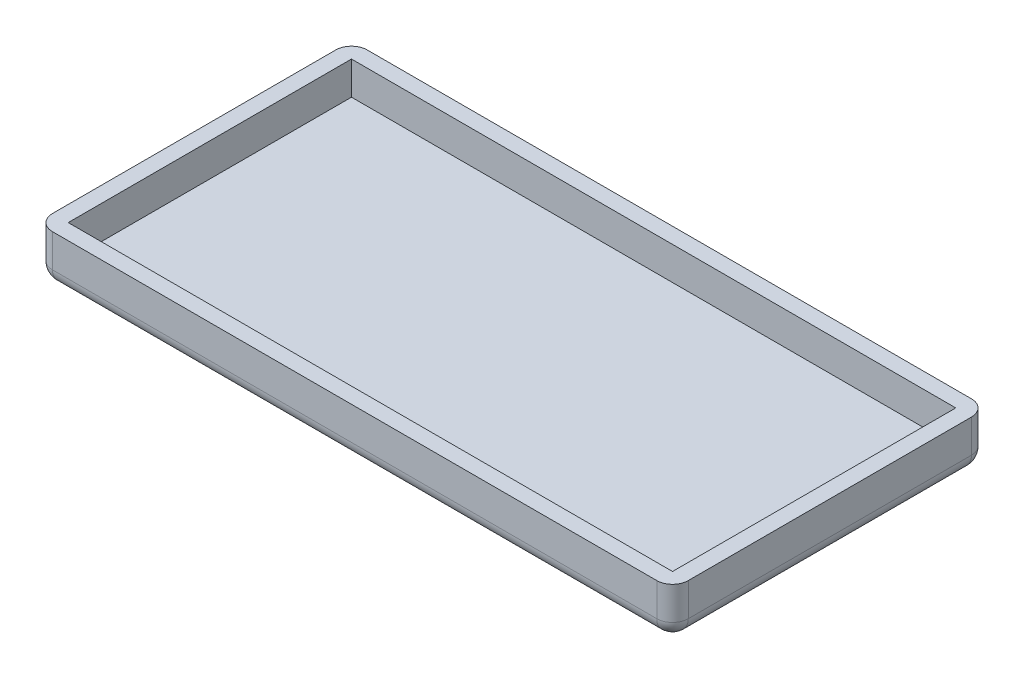
SolidWorks part; units mm, degrees
material "ABS"
ref_plane "Plan de face" through (0, 0, 0) normal (0, 0, 1) x (1, 0, 0)
ref_plane "Plan de dessus" through (0, 0, 0) normal (0, 1, 0) x (1, 0, 0)
ref_plane "Plan de droite" through (0, 0, 0) normal (1, 0, 0) x (0, 0, -1)
sketch "Esquisse1" plane through (0, 0, 0) normal (0, 1, 0) x (1, 0, 0)
  line L0 (-37.2093, 0) -> (46.3566, 0) construction
  line L2 (-25.5814, 10) -> (14.8186, 10)
  line L3 (-25.5814, 10) -> (-25.5814, -10)
  line L4 (-25.5814, -10) -> (14.8186, -10)
  line L5 (14.8186, 10) -> (14.8186, -10)
  dimension "D1" = 20
  dimension "D2" = 40.4
extrude "Boss.-Extru.1" add sketch "Esquisse1" along normal blind 1
sketch "Esquisse2" plane through (0, 1, 0) normal (0, 1, 0) x (1, 0, 0)
  line L0 (-24.5814, 9) -> (13.8186, 9)
  line L1 (-25.5814, 10) -> (14.8186, 10)
  line L2 (-25.5814, 10) -> (-25.5814, -10)
  line L3 (-25.5814, -10) -> (14.8186, -10)
  line L4 (14.8186, 10) -> (14.8186, -10)
  line L5 (13.8186, 9) -> (13.8186, -9)
  line L6 (-24.5814, -9) -> (13.8186, -9)
  line L7 (-24.5814, 9) -> (-24.5814, -9)
  dimension "D1" = 1
extrude "Boss.-Extru.2" add sketch "Esquisse2" along normal blind 2.1
fillet "Congé1" radius 1 8 edges at (-25.5814, 0, 0) (-25.5814, 1.55, -10) (-5.3814, 0, -10) (14.8186, 1.55, -10) (14.8186, 0, 0) (14.8186, 1.55, 10) (-5.3814, 0, 10) (-25.5814, 1.55, 10)
